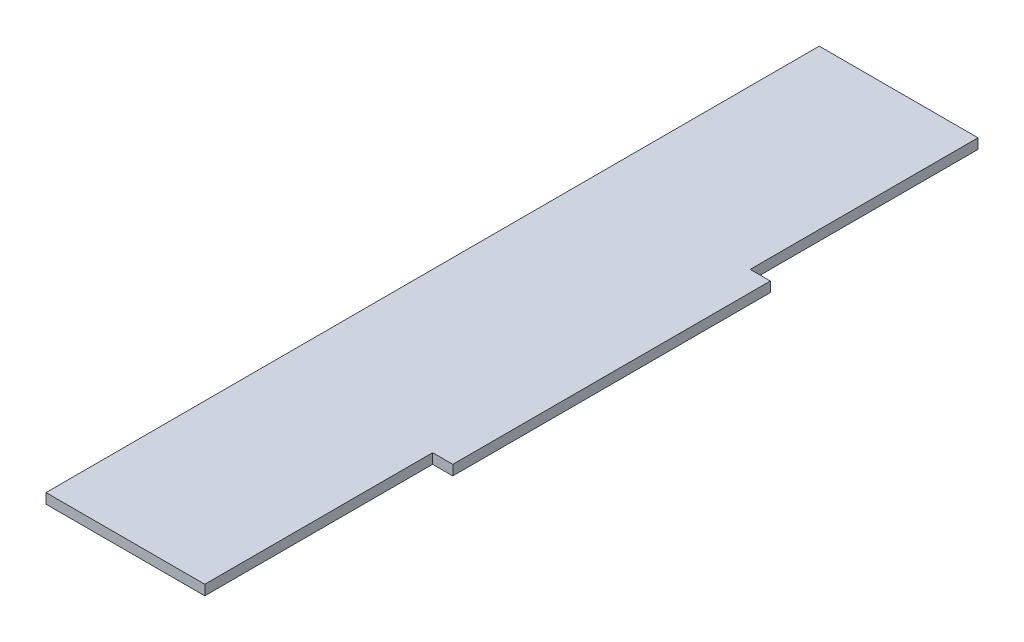
SolidWorks part; units mm, degrees
ref_plane "Front Plane" through (0, 0, 0) normal (0, 0, 1) x (1, 0, 0)
ref_plane "Top Plane" through (0, 0, 0) normal (0, 1, 0) x (1, 0, 0)
ref_plane "Right Plane" through (0, 0, 0) normal (1, 0, 0) x (0, 0, -1)
sketch "Sketch1" plane through (0, 0, 0) normal (0, 1, 0) x (1, 0, 0)
  line L0 (-25, 71.75) -> (25, 71.75)
  line L1 (25, 71.75) -> (25, 0)
  line L2 (25, 0) -> (31.35, 0)
  line L3 (31.35, 0) -> (31.35, -100)
  line L4 (31.35, -100) -> (25, -100)
  line L5 (25, -100) -> (25, -171.75)
  line L6 (25, -171.75) -> (-25, -171.75)
  line L7 (-25, -171.75) -> (-25, -100)
  line L8 (-25, -100) -> (-31.35, -100)
  line L9 (-31.35, -100) -> (-31.35, 0)
  line L10 (-31.35, 0) -> (-25, 0)
  line L11 (-25, 0) -> (-25, 71.75)
  line L12 (-25, 0) -> (-25, -100) construction
  point P11 (0, 71.75)
  point P14 (-31.35, -50)
  dimension "D1" = 6.35
  dimension "D2" = 100
  dimension "D3" = 50
  dimension "D4" = 243.5
extrude "Boss-Extrude1" add sketch "Sketch1" along normal blind 3.175 contours L11 L12 L7 L6 L5 L4 L3 L2 L1 L0
equation "\"length\"= 243.5mm"
equation "\"w_mach\"= 50mm"
equation "\"w_tab\"= 100mm"
equation "\"t_wood\"= 0.125in"
equation "\"t_side\"= 0.25in"
equation "\"D1@Sketch1\"=\"t_side\""
equation "\"D2@Sketch1\"=\"w_tab\""
equation "\"D3@Sketch1\"=\"w_mach\""
equation "\"D4@Sketch1\"=\"length\""
equation "\"D1@Boss-Extrude1\"=\"t_wood\""
